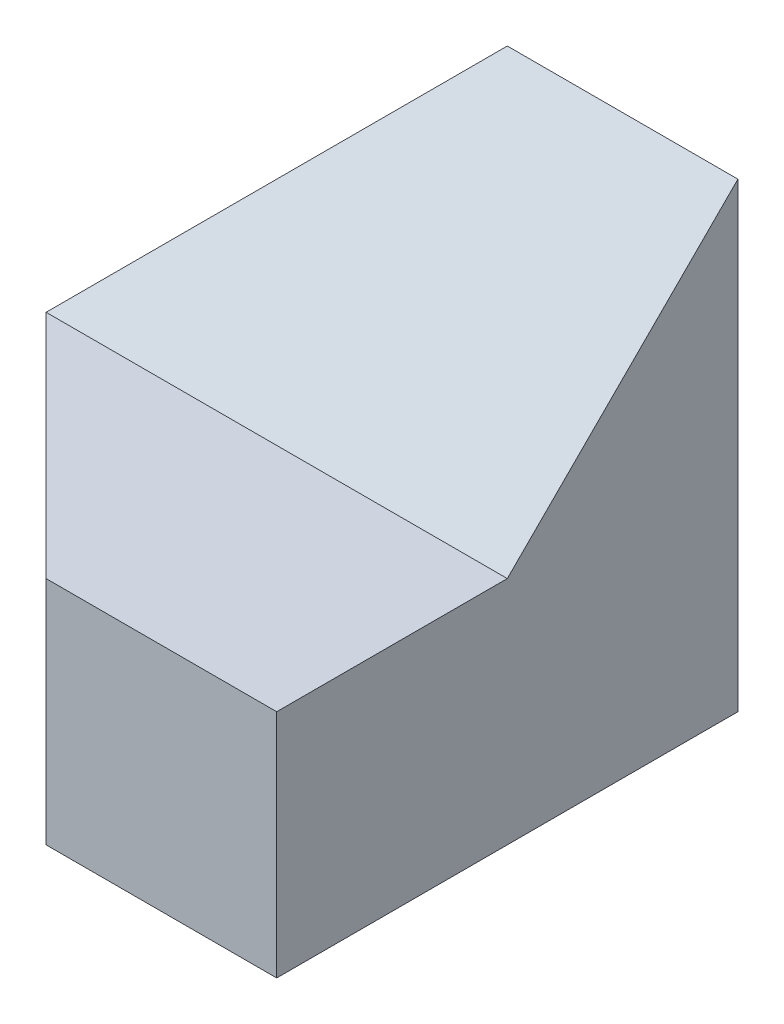
SolidWorks part; units mm, degrees
ref_plane "Front Plane" through (0, 0, 0) normal (0, 0, 1) x (1, 0, 0)
ref_plane "Top Plane" through (0, 0, 0) normal (0, 1, 0) x (1, 0, 0)
ref_plane "Right Plane" through (0, 0, 0) normal (1, 0, 0) x (0, 0, -1)
sketch "Sketch1" plane through (0, 0, 0) normal (0, 0, 1) x (1, 0, 0)
  line L1 (0, 0) -> (40, 0)
  line L2 (0, 0) -> (0, 40)
  line L3 (0, 40) -> (40, 40)
  line L4 (40, 0) -> (40, 40)
  dimension "D1" = 40
  dimension "D2" = 40
extrude "Boss-Extrude1" add sketch "Sketch1" along normal blind 40
sketch "Sketch2" plane through (0, 0, 40) normal (0, 0, 1) x (1, 0, 0)
  line L0 (0, 20) -> (0, 40)
  line L1 (0, 40) -> (0, 0) construction
  line L2 (0, 40) -> (20, 40)
  line L3 (40, 40) -> (0, 40) construction
  line L4 (20, 40) -> (0, 20)
extrude "Cut-Extrude1" cut sketch "Sketch2" against normal blind 40
sketch "Sketch3" plane through (0, 0, 0) normal (-1, 0, 0) x (0, 0, 1)
  line L0 (40, 20) -> (20, 20)
  line L1 (0, 20) -> (40, 20) construction
  line L2 (20, 20) -> (0, 40)
  line L3 (0, 40) -> (40, 40)
  line L4 (40, 40) -> (40, 20)
  dimension "D1" = 40
  dimension "D2" = 20
extrude "Cut-Extrude2" cut sketch "Sketch3" against normal blind 40
sketch "Sketch4" plane through (0, 20, 0) normal (0, 1, 0) x (1, 0, 0)
  line L0 (0, -20) -> (20, -40)
  line L1 (40, -40) -> (0, -40) construction
  line L2 (20, -40) -> (0, -40)
  line L3 (0, -40) -> (0, -20)
extrude "Cut-Extrude3" cut sketch "Sketch4" against normal blind 40
